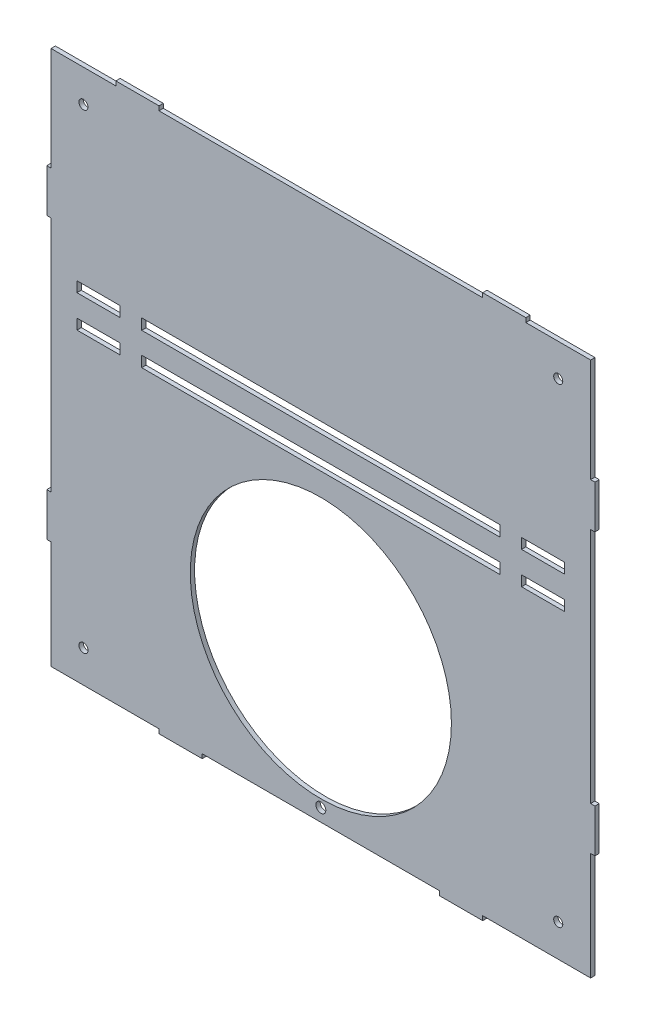
SolidWorks part; units mm, degrees
ref_plane "Front Plane" through (0, 0, 0) normal (0, 0, 1) x (1, 0, 0)
ref_plane "Top Plane" through (0, 0, 0) normal (0, 1, 0) x (1, 0, 0)
ref_plane "Right Plane" through (0, 0, 0) normal (1, 0, 0) x (0, 0, -1)
sketch "Sketch1" plane through (0, 0, 0) normal (0, 0, 1) x (1, 0, 0)
  line L0 (-127, -19.9) -> (-125, -19.9) construction
  line L1 (125, -69.9) -> (75, -69.9)
  line L2 (125, -69.9) -> (125, -19.9)
  line L3 (125, 180.1) -> (-125, 180.1)
  line L4 (-125, -69.9) -> (-125, -19.9)
  line L5 (-127, 0.1) -> (-127, -19.9) construction
  line L6 (-125, 0.1) -> (-127, 0.1) construction
  line L7 (-127, 110.1) -> (-125, 110.1) construction
  line L8 (-127, 130.1) -> (-127, 110.1) construction
  line L9 (-125, 130.1) -> (-127, 130.1) construction
  line L10 (125, 130.1) -> (127, 130.1) construction
  line L11 (127, 130.1) -> (127, 110.1) construction
  line L12 (127, 110.1) -> (125, 110.1) construction
  line L13 (127, -19.9) -> (125, -19.9) construction
  line L14 (127, 0.1) -> (127, -19.9) construction
  line L15 (125, 0.1) -> (127, 0.1) construction
  line L16 (-127, -19.9) -> (-125, -19.9)
  line L17 (-127, 0.1) -> (-127, -19.9)
  line L18 (-125, 0.1) -> (-127, 0.1)
  line L19 (-127, 110.1) -> (-125, 110.1)
  line L20 (-127, 130.1) -> (-127, 110.1)
  line L21 (-125, 130.1) -> (-127, 130.1)
  line L22 (125, 130.1) -> (127, 130.1)
  line L23 (127, 130.1) -> (127, 110.1)
  line L24 (127, 110.1) -> (125, 110.1)
  line L25 (127, -19.9) -> (125, -19.9)
  line L26 (127, 0.1) -> (127, -19.9)
  line L27 (125, 0.1) -> (127, 0.1)
  line L31 (-55, -71.9) -> (-55, -69.9) construction
  line L33 (-75, -71.9) -> (-75, -69.9) construction
  line L34 (55, -71.9) -> (55, -69.9)
  line L35 (-55, -71.9) -> (-75, -71.9)
  line L36 (75, -71.9) -> (75, -69.9)
  line L37 (-55, -71.9) -> (-55, -69.9)
  line L38 (75, -71.9) -> (55, -71.9)
  line L39 (-75, -71.9) -> (-75, -69.9)
  line L40 (-125, 180.1) -> (125, 180.1) construction
  line L41 (-125, 130.1) -> (-125, 180.1)
  line L42 (125, 130.1) -> (125, 180.1)
  line L43 (125, 0.1) -> (125, 110.1)
  line L44 (55, -69.9) -> (-55, -69.9)
  line L45 (-75, -69.9) -> (-125, -69.9)
  line L46 (-125, 0.1) -> (-125, 110.1)
  circle A0 centre (0, 0) radius 57.5 construction
  circle A1 centre (0, 0) radius 57.5 construction
  circle A2 centre (0, 0) radius 60.5
  circle A3 centre (0, -64) radius 2.3 construction
  circle A4 centre (0, -64) radius 2.3
  dimension "D3" = 20
  dimension "D1" = 0
  dimension "D2" = 3
  dimension "D4" = 2
  dimension "D5" = 50
extrude "Boss-Extrude1" add sketch "Sketch1" along normal blind 2
sketch "Sketch3" plane through (0, 0, 2) normal (0, 0, 1) x (1, 0, 0)
  line L0 (-113, 91.0052) -> (-113, 86.0052) construction
  line L1 (-113, 90.9052) -> (-93, 90.9052)
  line L2 (-113, 90.9052) -> (-113, 86.1052)
  line L3 (-113, 86.1052) -> (-93, 86.1052)
  line L4 (-93, 90.9052) -> (-93, 86.1052)
  line L5 (-93, 91.0052) -> (-93, 86.0052) construction
  line L6 (-113, 86.0052) -> (-93, 86.0052) construction
  line L7 (-113, 76.0052) -> (-113, 71.0052) construction
  line L8 (-113, 75.9052) -> (-93, 75.9052)
  line L9 (-113, 75.9052) -> (-113, 71.1052)
  line L10 (-113, 71.1052) -> (-93, 71.1052)
  line L11 (-93, 75.9052) -> (-93, 71.1052)
  line L12 (-93, 76.0052) -> (-93, 71.0052) construction
  line L13 (-113, 71.0052) -> (-93, 71.0052) construction
  dimension "D1" = 4.8
  dimension "D2" = 0.1
  dimension "D3" = 0.1
  dimension "D4" = 4.8
extrude "Cut-Extrude1" cut sketch "Sketch3" against normal blind 5
mirror "Mirror1" about plane through (0, 0, 0) normal (1, 0, 0) of "Cut-Extrude1"
sketch "Sketch4" plane through (0, 0, 2) normal (0, 0, 1) x (1, 0, 0)
  line L0 (60.3848, 86.0052) -> (80.6469, 86.0052) construction
  line L1 (-83, 91.0052) -> (83, 91.0052)
  line L2 (-83, 91.0052) -> (-83, 86.0052)
  line L3 (-83, 86.0052) -> (83, 86.0052)
  line L4 (83, 91.0052) -> (83, 86.0052)
  line L5 (93, 91.0052) -> (93, 86.0052) construction
  line L6 (-93, 91.0052) -> (-93, 86.0052) construction
  line L7 (-93, 76.0052) -> (-80.6469, 76.0052) construction
  line L8 (-83, 76.0052) -> (83, 76.0052)
  line L9 (-83, 76.0052) -> (-83, 71.0052)
  line L10 (-83, 71.0052) -> (83, 71.0052)
  line L11 (83, 76.0052) -> (83, 71.0052)
  line L12 (80.6469, 71.0052) -> (93, 71.0052) construction
  dimension "D1" = 5
  dimension "D2" = 10
  dimension "D3" = 10
  dimension "D4" = 5
extrude "Cut-Extrude2" cut sketch "Sketch4" against normal blind 5
sketch "Sketch5" plane through (0, 0, 2) normal (0, 0, 1) x (1, 0, 0)
  line L0 (-125, -69.9) -> (-75, -69.9) construction
  line L1 (-125, -19.9) -> (-125, -69.9) construction
  line L2 (75, -69.9) -> (125, -69.9) construction
  line L3 (125, -69.9) -> (125, -19.9) construction
  circle A0 centre (-110, -54.9) radius 2.1
  circle A1 centre (110, -54.9) radius 2.1
  dimension "D1" = 4.2
  dimension "D2" = 15
  dimension "D3" = 15
  dimension "D4" = 4.2
  dimension "D5" = 15
  dimension "D6" = 15
extrude "Cut-Extrude3" cut sketch "Sketch5" against normal blind 5
sketch "Sketch6" plane through (0, 0, 2) normal (0, 0, 1) x (1, 0, 0)
  line L0 (-125, 178.1) -> (-95, 178.1)
  line L1 (-125, -74.1) -> (-125, 180.1) construction
  line L2 (-95, 178.1) -> (-95, 180.1)
  line L3 (125, 180.1) -> (-125, 180.1) construction
  line L4 (-75, 180.1) -> (-75, 178.1)
  line L5 (-75, 178.1) -> (75, 178.1)
  line L6 (75, 178.1) -> (75, 180.1)
  line L7 (95, 180.1) -> (95, 178.1)
  line L8 (95, 178.1) -> (125, 178.1)
  line L9 (125, -74.1) -> (125, 180.1) construction
  line L10 (125, 178.1) -> (125, 180.1)
  line L11 (125, 180.1) -> (95, 180.1)
  line L12 (-125, 180.1) -> (-125, 130.1) construction
  line L13 (-125, 178.1) -> (-125, 180.1)
  line L14 (-125, 180.1) -> (-95, 180.1)
  line L15 (-75, 180.1) -> (75, 180.1)
  dimension "D1" = 20
  dimension "D2" = 2
  dimension "D3" = 20
  dimension "D4" = 30
  dimension "D5" = 30
extrude "Cut-Extrude4" cut sketch "Sketch6" against normal blind 5
sketch "Sketch7" plane through (0, 0, 2) normal (0, 0, 1) x (1, 0, 0)
  line L0 (-125, 178.1) -> (-125, 130.1) construction
  line L1 (-125, 178.1) -> (-95, 178.1) construction
  line L2 (125, 130.1) -> (125, 178.1) construction
  line L3 (95, 178.1) -> (125, 178.1) construction
  circle A0 centre (-110, 163.1) radius 2.1
  circle A1 centre (110, 163.1) radius 2.1
  dimension "D1" = 4.2
  dimension "D2" = 4.2
  dimension "D3" = 15
  dimension "D5" = 15
  dimension "D6" = 15
  dimension "D4" = 15
extrude "Cut-Extrude5" cut sketch "Sketch7" against normal blind 5
